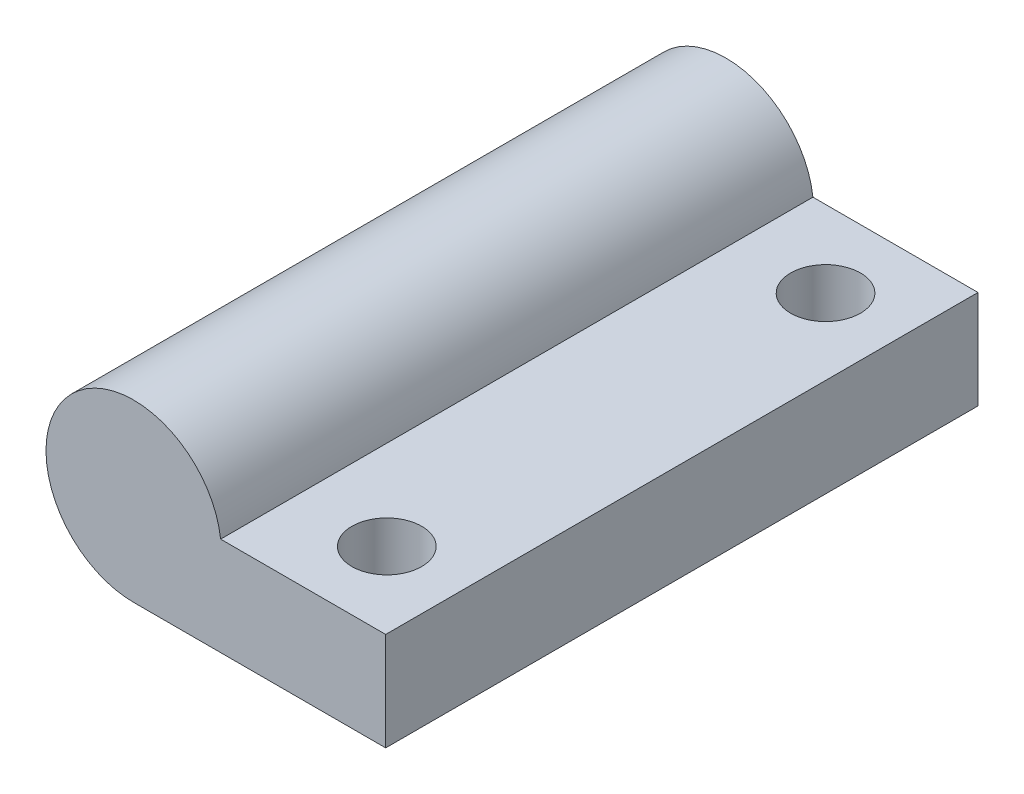
SolidWorks part; units mm, degrees
ref_plane "Front Plane" through (0, 0, 0) normal (0, 0, 1) x (1, 0, 0)
ref_plane "Top Plane" through (0, 0, 0) normal (0, 1, 0) x (1, 0, 0)
ref_plane "Right Plane" through (0, 0, 0) normal (1, 0, 0) x (0, 0, -1)
sketch "Sketch1" plane through (0, 0, 0) normal (0, 0, 1) x (1, 0, 0)
  line L0 (-19.0864, 25.7218) -> (-0.9106, 25.7218)
  line L1 (-0.9106, 25.7218) -> (-0.9106, 32.8338)
  line L2 (-0.9106, 32.8338) -> (-12.8546, 32.8338)
  arc A1 (-12.8546, 32.8338) -> (-19.0864, 25.7218) centre (-19.1497, 32.0636) ccw
  dimension "D1" = 7.112
extrude "Boss-Extrude1" add sketch "Sketch1" along normal blind 42.8625
hole_wizard "#8 (0.199) Diameter Hole1" positions "Sketch4" profile "Sketch3" hole size "#8" standard "Ansi Inch"
sketch "Sketch4" plane through (0, 32.8338, 0) normal (0, 1, 0) x (-1, 0, 0)
  line L0 (0.9106, 0) -> (12.8546, 0) construction
  line L1 (19.0864, 42.8625) -> (19.0864, 0) construction
  point P0 (6.3864, 37.3062)
  point P1 (6.3864, 5.5562)
  dimension "D1" = 31.75
  dimension "D2" = 5.5562
  dimension "D3" = 12.7
  dimension "D4" = 12.7
sketch "Sketch3" plane through (-6.3864, 32.8338, 37.3062) normal (1, 0, 0) x (0, 0, 1)
  line L0 (0, 0) -> (0, 7.8686)
  line L1 (0, 7.8686) -> (2.5273, 6.35)
  line L2 (2.5273, 6.35) -> (2.5273, 0)
  line L5 (2.5273, 0) -> (0, 0)
  line L10 (0, 7.8686) -> (-2.5273, 6.35) construction
  line L11 (0, -6.35) -> (0, 107.95) construction
  dimension "Hole Dia." = 5.0546
  dimension "Hole Depth" = 6.35
  dimension "Drill Angle" = 118
equation "\"D2@Sketch4\" = (\"RD1@Annotations\"-\"D1@Sketch4\")/2"
